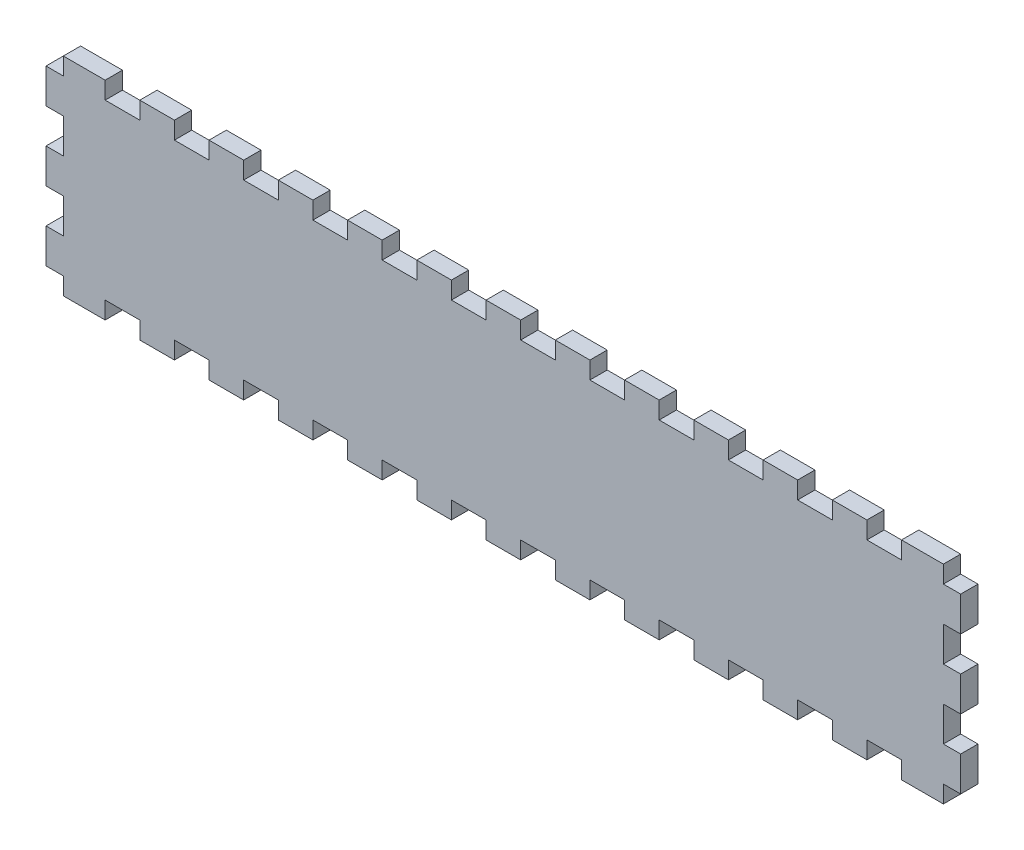
SolidWorks part; units mm, degrees
ref_plane "Front Plane" through (0, 0, 0) normal (0, 0, 1) x (1, 0, 0)
ref_plane "Top Plane" through (0, 0, 0) normal (0, 1, 0) x (1, 0, 0)
ref_plane "Right Plane" through (0, 0, 0) normal (1, 0, 0) x (0, 0, -1)
sketch "Sketch2" plane through (0, 0, 0) normal (0, 0, 1) x (1, 0, 0)
  line L0 (-152.5, 6) -> (-152.5, 0)
  line L1 (-152.5, 0) -> (-158.5, 0)
  line L2 (-158.5, 0) -> (-158.5, -12)
  line L3 (-158.5, -12) -> (-152.5, -12)
  line L4 (-152.5, -12) -> (-152.5, -24)
  line L5 (-152.5, -24) -> (-158.5, -24)
  line L6 (-158.5, -24) -> (-158.5, -36)
  line L7 (-152.5, -36) -> (-158.5, -36) construction
  line L8 (-158.5, -36) -> (-152.5, -36)
  line L9 (-152.5, -36) -> (-152.5, -48)
  line L10 (-152.5, -48) -> (-158.5, -48)
  line L11 (-158.5, -48) -> (-158.5, -60)
  line L12 (-158.5, -60) -> (-152.5, -60)
  line L13 (-152.5, -60) -> (-152.5, -66)
  line L15 (-152.5, 6) -> (-138, 6)
  line L16 (-138, 6) -> (-138, 0)
  line L17 (-138, 0) -> (-126, 0)
  line L18 (-126, 0) -> (-126, 6)
  line L19 (-126, 6) -> (-114, 6)
  line L20 (-114, 6) -> (-114, 0)
  line L21 (-114, 0) -> (-102, 0)
  line L22 (-102, 0) -> (-102, 6)
  line L23 (-102, 6) -> (-90, 6)
  line L24 (-90, 6) -> (-90, 0)
  line L25 (-102, 0) -> (-90, 0) construction
  line L26 (-90, 0) -> (-78, 0)
  line L27 (-78, 0) -> (-78, 6)
  line L28 (-78, 6) -> (-66, 6)
  line L29 (-66, 6) -> (-66, 0)
  line L30 (-66, 0) -> (-54, 0)
  line L31 (-54, 0) -> (-54, 6)
  line L32 (-54, 6) -> (-54, 0) construction
  line L33 (-54, 6) -> (-42, 6)
  line L34 (-54, 6) -> (-42, 6) construction
  line L35 (-42, 6) -> (-42, 0)
  line L36 (-42, 0) -> (-30, 0)
  line L37 (-30, 0) -> (-30, 6)
  line L38 (-30, 6) -> (-18, 6)
  line L39 (-18, 6) -> (-18, 0)
  line L40 (-18, 0) -> (-6, 0)
  line L41 (-6, 0) -> (-6, 6)
  line L42 (-6, 6) -> (6, 6)
  line L43 (6, 6) -> (6, 0)
  line L44 (6, 0) -> (18, 0)
  line L45 (18, 0) -> (18, 6)
  line L46 (18, 6) -> (30, 6)
  line L47 (30, 6) -> (30, 0)
  line L48 (30, 0) -> (42, 0)
  line L49 (42, 0) -> (42, 6)
  line L50 (42, 6) -> (54, 6)
  line L51 (54, 6) -> (54, 0)
  line L52 (54, 0) -> (66, 0)
  line L53 (66, 0) -> (66, 6)
  line L54 (66, 6) -> (78, 6)
  line L55 (78, 6) -> (78, 0)
  line L56 (78, 0) -> (90, 0)
  line L57 (90, 0) -> (90, 6)
  line L58 (90, 6) -> (102, 6)
  line L59 (102, 6) -> (102, 0)
  line L60 (102, 0) -> (114, 0)
  line L61 (114, 0) -> (114, 6)
  line L62 (114, 6) -> (126, 6)
  line L63 (126, 6) -> (126, 0)
  line L64 (126, 0) -> (138, 0)
  line L65 (138, 0) -> (138, 6)
  line L66 (138, 6) -> (152.5, 6)
  line L67 (152.5, 6) -> (152.5, 0)
  line L68 (152.5, 0) -> (158.5, 0)
  line L69 (158.5, 0) -> (158.5, -12)
  line L70 (158.5, -12) -> (152.5, -12)
  line L71 (152.5, -12) -> (152.5, -24)
  line L72 (152.5, -24) -> (158.5, -24)
  line L73 (158.5, -24) -> (158.5, -36)
  line L74 (158.5, -36) -> (152.5, -36)
  line L75 (152.5, -36) -> (152.5, -48)
  line L76 (152.5, -48) -> (158.5, -48)
  line L77 (158.5, -48) -> (158.5, -60)
  line L78 (158.5, -60) -> (152.5, -60)
  line L79 (152.5, -60) -> (152.5, -66)
  line L81 (-152.5, -66) -> (-138, -66)
  line L82 (-138, -66) -> (-138, -60)
  line L83 (-138, -60) -> (-126, -60)
  line L84 (-126, -60) -> (-126, -66)
  line L85 (-126, -66) -> (-114, -66)
  line L86 (-114, -66) -> (-114, -60)
  line L87 (-114, -60) -> (-102, -60)
  line L88 (-102, -60) -> (-102, -66)
  line L89 (-102, -66) -> (-90, -66)
  line L90 (-90, -66) -> (-90, -60)
  line L91 (-90, -60) -> (-78, -60)
  line L92 (-78, -60) -> (-78, -66)
  line L93 (-78, -66) -> (-66, -66)
  line L94 (-66, -66) -> (-66, -60)
  line L95 (-66, -60) -> (-54, -60)
  line L96 (-54, -60) -> (-54, -66)
  line L97 (-54, -66) -> (-42, -66)
  line L98 (-42, -66) -> (-42, -60)
  line L99 (-42, -60) -> (-30, -60)
  line L100 (-30, -60) -> (-30, -66)
  line L101 (-30, -66) -> (-18, -66)
  line L102 (-18, -66) -> (-18, -60)
  line L103 (-18, -60) -> (-6, -60)
  line L104 (-6, -60) -> (-6, -66)
  line L105 (-6, -66) -> (6, -66)
  line L106 (6, -66) -> (6, -60)
  line L107 (6, -60) -> (18, -60)
  line L108 (18, -60) -> (18, -66)
  line L109 (18, -66) -> (30, -66)
  line L110 (30, -66) -> (30, -60)
  line L111 (30, -60) -> (42, -60)
  line L112 (42, -60) -> (42, -66)
  line L113 (42, -66) -> (54, -66)
  line L114 (54, -66) -> (54, -60)
  line L115 (54, -60) -> (66, -60)
  line L116 (66, -60) -> (66, -66)
  line L117 (66, -66) -> (78, -66)
  line L118 (78, -66) -> (78, -60)
  line L119 (78, -60) -> (90, -60)
  line L120 (90, -60) -> (90, -66)
  line L121 (90, -66) -> (102, -66)
  line L122 (102, -66) -> (102, -60)
  line L123 (102, -60) -> (114, -60)
  line L124 (114, -60) -> (114, -66)
  line L125 (114, -66) -> (126, -66)
  line L126 (126, -66) -> (126, -60)
  line L127 (126, -60) -> (138, -60)
  line L128 (138, -60) -> (138, -66)
  line L129 (138, -66) -> (152.5, -66)
extrude "Boss-Extrude5" add sketch "Sketch2" along normal blind 6 contours L129 L79 L78 L77 L76 L75 L74 L73 L72 L71 L70 L69 L68 L67 L66 L65 L64 L63 L62 L61 L60 L59 L58 L57 L56 L55 L54 L53 L52 L51 L50 L49 L48 L47 L46 L45 L44 L43 L42 L41 L40 L39 L38 L37 L36 L35 L33 L31 L30 L29 L28 L27 L26 L24 L23 L22 L21 L20 L19 L18 L17 L16 L15 L0 L1 L2 L3 L4 L5 L6 L8 L9 L10 L11 L12 L13 L81 L82 L83 L84 L85 L86 L87 L88 L89 L90 L91 L92 L93 L94 L95 L96 L97 L98 L99 L100 L101 L102 L103 L104 L105 L106 L107 L108 L109 L110 L111 L112 L113 L114 L115 L116 L117 L118 L119 L120 L121 L122 L123 L124 L125 L126 L127 L128
